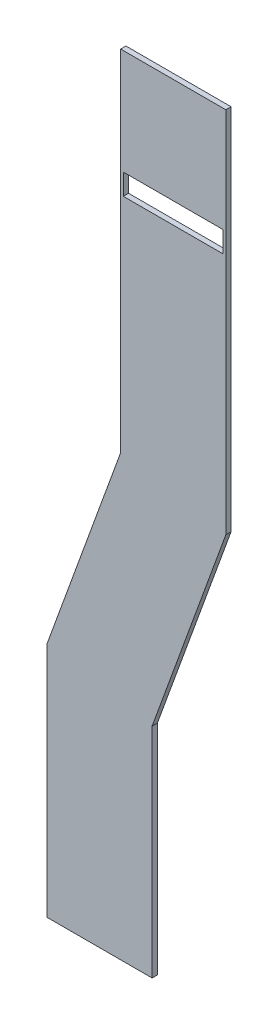
SolidWorks part; units mm, degrees
ref_plane "Front Plane" through (0, 0, 0) normal (0, 0, 1) x (1, 0, 0)
ref_plane "Top Plane" through (0, 0, 0) normal (0, 1, 0) x (1, 0, 0)
ref_plane "Right Plane" through (0, 0, 0) normal (1, 0, 0) x (0, 0, -1)
sketch "Sketch1" plane through (0, 0, 0) normal (0, 0, 1) x (1, 0, 0)
  line L1 (0, 0) -> (-20, 0)
  line L2 (-20, 0) -> (-20, -66.4735)
  line L3 (-20, -66.4735) -> (-34.0225, -105)
  line L4 (-34.0225, -105) -> (-34.0225, -150)
  line L5 (-34.0225, -150) -> (-14.0225, -150)
  line L6 (-14.0225, -150) -> (-14.0225, -108.5265)
  line L7 (-14.0225, -108.5265) -> (0, -70)
  line L8 (0, -70) -> (0, 0)
  point P1 (0, 0)
  point P4 (-29.1723, -7.2694)
  point P11 (0, 0)
  point P12 (0, 0)
  point P14 (0, 0)
  point P19 (-3.161, 74.8536)
  dimension "D1" = 0
  dimension "D2" = 0
  dimension "D3" = 70
  dimension "D4" = 160
  dimension "D5" = 20
  dimension "D6" = 20
  dimension "D7" = 150
  dimension "D8" = 45
  dimension "D9" = 20
extrude "Boss-Extrude1" add sketch "Sketch1" along normal blind 1
sketch "Sketch2" plane through (0, 0, 0) normal (0, 0, -1) x (-1, 0, 0)
  line L0 (0.5, -20) -> (0.5, -24)
  line L1 (0.5, -24) -> (19.5, -24)
  line L2 (19.5, -24) -> (19.5, -20)
  line L3 (19.5, -20) -> (0.5, -20)
  line L4 (0, -70) -> (0, 0) construction
  line L6 (0, 0) -> (20, 0) construction
  dimension "D1" = 4
  dimension "D2" = 19
  dimension "D3" = 0.5
  dimension "D4" = 20
extrude "Cut-Extrude1" cut sketch "Sketch2" against normal up to surface (1 mm away) contours L3 L0 L1 L2 up to face at (-17.0113, -81.25, 1)
